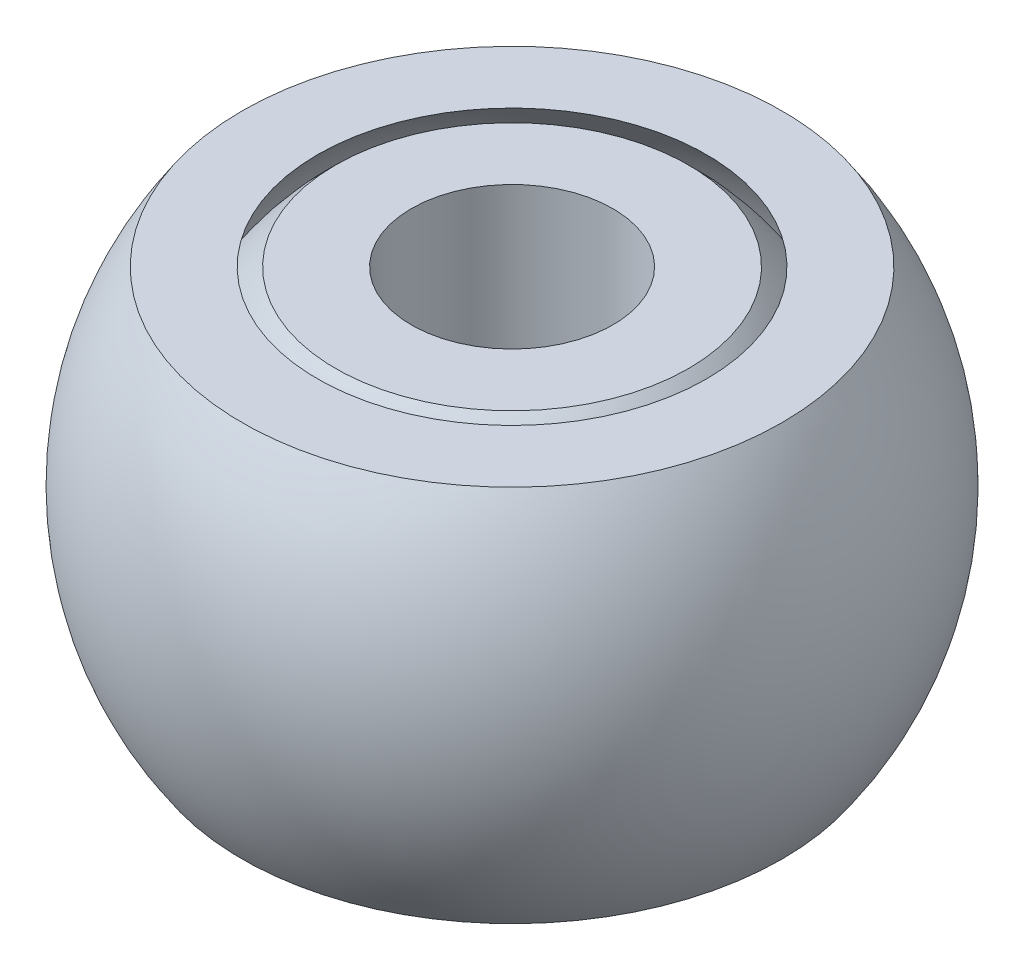
SolidWorks part; units mm, degrees
ref_plane "Alzado" through (0, 0, 0) normal (0, 0, 1) x (1, 0, 0)
ref_plane "Planta" through (0, 0, 0) normal (0, 1, 0) x (1, 0, 0)
ref_plane "Vista lateral" through (0, 0, 0) normal (1, 0, 0) x (0, 0, -1)
sketch "Croquis2" plane through (0, 0, 0) normal (0, 0, 1) x (1, 0, 0)
  line L0 (0, 7.5) -> (0, -7.5) construction
  line L1 (0, 7.5) -> (-7, 7.5) construction
  line L3 (-7, 7.5) -> (-10.5973, 7.5) construction
  line L4 (-7.7142, 7.5) -> (-10.7142, 7.5)
  line L5 (0, 0) -> (-10.2591, 0) construction
  line L6 (-7.7142, -7.5) -> (-10.7142, -7.5)
  line L7 (-4, 7.5) -> (-4, -7.5)
  line L8 (-7, 7.5) -> (-4, 7.5)
  line L9 (-7, -7.5) -> (-4, -7.5)
  line L10 (-13.0784, 0) -> (-13.0784, 7.5) construction
  arc A0 (-7, 7.5) -> (-7, -7.5) centre (0, 0) ccw
  arc A1 (-7.7142, 7.5) -> (-7.7142, -7.5) centre (0, 0) ccw
  arc A2 (-10.7142, 7.5) -> (-10.7142, -7.5) centre (0, 0) ccw
  point P3 (0, 0)
  dimension "D2" = 0.5
  dimension "D1" = 15
  dimension "D3" = 4
  dimension "D4" = 3
  dimension "D5" = 3
revolve "Revolución1" add sketch "Croquis2" angle 360 about L0
ref_plane "Plano1" through (-13.0784, 0, 0) normal (1, 0, 0) x (0, 0, -1)
sketch "Croquis3" plane through (-13.0784, 0, 0) normal (1, 0, 0) x (0, 0, -1)
  line L1 (3.5, 3.5) -> (-3.5, 3.5)
  line L2 (3.5, 3.5) -> (3.5, -3.5)
  line L3 (3.5, -3.5) -> (-3.5, -3.5)
  line L4 (-3.5, 3.5) -> (-3.5, -3.5)
  point P4 (0, 3.5)
  point P6 (-3.5, 0)
  dimension "D1" = 7
  dimension "D2" = 7
extrude "Cortar-Extruir1" cut sketch "Croquis3" along normal blind 1
